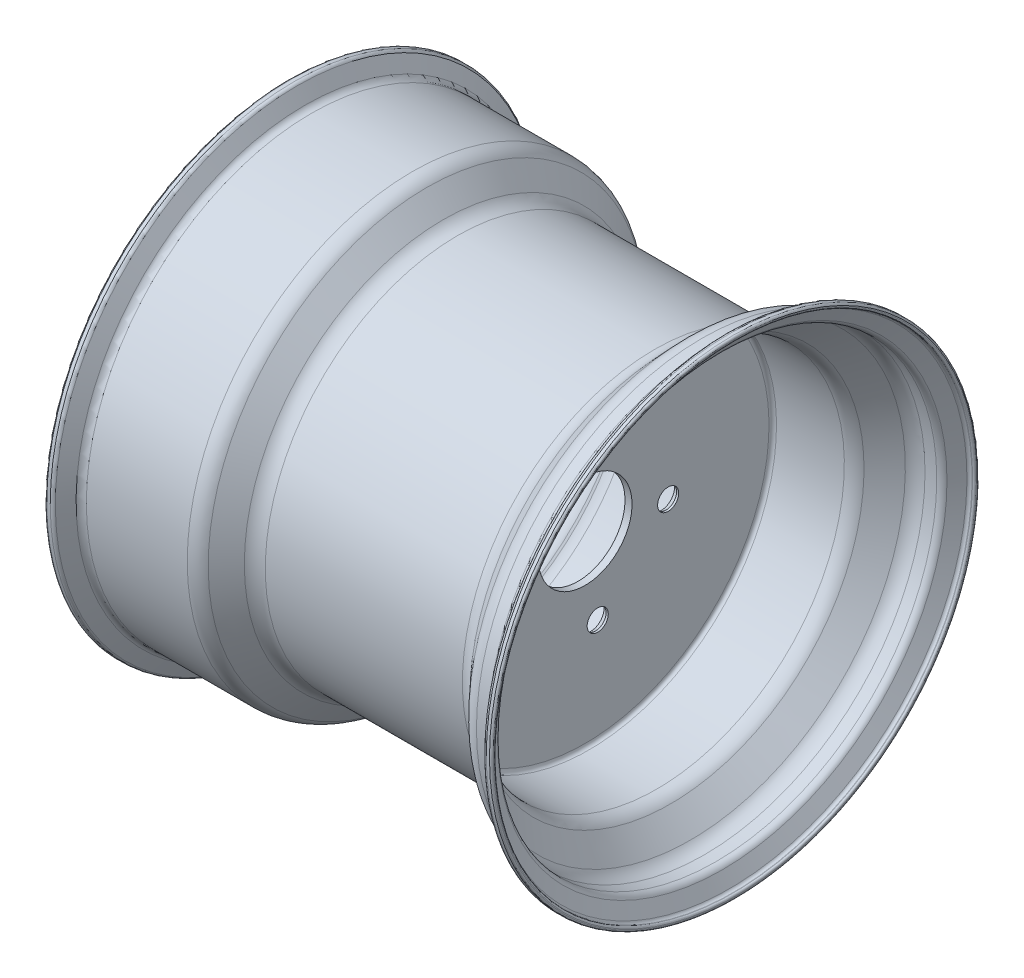
SolidWorks part; units mm, degrees
material "1060 Alloy"
ref_plane "Front Plane" through (0, 0, 0) normal (0, 0, 1) x (1, 0, 0)
ref_plane "Top Plane" through (0, 0, 0) normal (0, 1, 0) x (1, 0, 0)
ref_plane "Right Plane" through (0, 0, 0) normal (1, 0, 0) x (0, 0, -1)
sketch "Sketch1" plane through (0, 0, 0) normal (0, 0, 1) x (1, 0, 0)
  line L0 (-81.5771, 130.175) -> (51.8349, 130.175)
  line L2 (0, 124.46) -> (0, 0)
  line L3 (-84.533, 127) -> (-2.54, 127)
  line L4 (-105.4345, 144.7317) -> (-94.2253, 131.4933)
  line L5 (-182.3188, 149.225) -> (-115.1268, 149.225)
  line L6 (-102.4786, 147.9067) -> (-91.2694, 134.6683)
  line L7 (-194.5586, 161.925) -> (-194.0506, 161.925)
  line L8 (-195.8286, 163.83) -> (-195.8286, 163.195)
  line L9 (-192.2175, 165.1) -> (-194.5586, 165.1)
  line L10 (-184.8852, 154.94) -> (-190.0178, 163.83)
  line L11 (-112.1709, 152.4) -> (-180.4858, 152.4)
  line L12 (61.123, 134.2136) -> (74.6121, 148.6789)
  line L13 (83.9003, 152.7175) -> (91.3853, 152.7175)
  line L14 (95.7847, 155.2575) -> (100.734, 163.83)
  line L15 (102.9337, 165.1) -> (105.0925, 165.1)
  line L16 (106.3625, 163.83) -> (106.3625, 163.195)
  line L17 (105.0925, 161.925) -> (104.7668, 161.925)
  line L18 (102.5671, 160.655) -> (97.6177, 152.0825)
  line L19 (93.2183, 149.5425) -> (85.2808, 149.5425)
  line L20 (75.9926, 145.5039) -> (62.5036, 131.0386)
  line L21 (53.2154, 127) -> (7.3025, 127)
  line L22 (4.7625, 124.46) -> (4.7625, 0)
  line L23 (4.7625, 0) -> (0, 0)
  line L26 (-191.8509, 160.655) -> (-186.7182, 151.765)
  arc A0 (106.3625, 163.195) -> (105.0925, 161.925) centre (105.0925, 163.195) cw
  arc A1 (105.0925, 165.1) -> (106.3625, 163.83) centre (105.0925, 163.83) cw
  arc A2 (-194.5586, 161.925) -> (-195.8286, 163.195) centre (-194.5586, 163.195) cw
  arc A3 (-195.8286, 163.83) -> (-194.5586, 165.1) centre (-194.5586, 163.83) cw
  arc A4 (-192.2175, 165.1) -> (-190.0178, 163.83) centre (-192.2175, 162.56) cw
  arc A5 (-191.8509, 160.655) -> (-194.0506, 161.925) centre (-194.0506, 159.385) ccw
  arc A6 (104.7668, 161.925) -> (102.5671, 160.655) centre (104.7668, 159.385) ccw
  arc A7 (100.734, 163.83) -> (102.9337, 165.1) centre (102.9337, 162.56) cw
  arc A8 (62.5036, 131.0386) -> (53.2154, 127) centre (53.2154, 139.7) cw
  arc A9 (51.8349, 130.175) -> (61.123, 134.2136) centre (51.8349, 142.875) ccw
  arc A10 (74.6121, 148.6789) -> (83.9003, 152.7175) centre (83.9003, 140.0175) cw
  arc A11 (85.2808, 149.5425) -> (75.9926, 145.5039) centre (85.2808, 136.8425) ccw
  arc A12 (97.6177, 152.0825) -> (93.2183, 149.5425) centre (93.2183, 154.6225) cw
  arc A13 (91.3853, 152.7175) -> (95.7847, 155.2575) centre (91.3853, 157.7975) ccw
  arc A14 (-102.4786, 147.9067) -> (-112.1709, 152.4) centre (-112.1709, 139.7) ccw
  arc A15 (-184.8852, 154.94) -> (-180.4858, 152.4) centre (-180.4858, 157.48) ccw
  arc A16 (-81.5771, 130.175) -> (-91.2694, 134.6683) centre (-81.5771, 142.875) cw
  arc A17 (-84.533, 127) -> (-94.2253, 131.4933) centre (-84.533, 139.7) cw
  arc A18 (-105.4345, 144.7317) -> (-115.1268, 149.225) centre (-115.1268, 136.525) ccw
  arc A20 (7.3025, 127) -> (4.7625, 124.46) centre (7.3025, 124.46) ccw
  arc A21 (0, 124.46) -> (-2.54, 127) centre (-2.54, 124.46) ccw
  arc A22 (-182.3188, 149.225) -> (-186.7182, 151.765) centre (-182.3188, 154.305) cw
  point P29 (106.3625, 161.925)
  point P32 (106.3625, 165.1)
  point P43 (103.3003, 161.925)
  point P48 (58.7375, 127)
  point P53 (78.3782, 152.7175)
  point P56 (79.7587, 149.5425)
  point P59 (96.1513, 149.5425)
  point P62 (94.3182, 152.7175)
  point P68 (-183.4187, 152.4)
  point P71 (-98.4276, 130.175)
  point P74 (-90.4207, 127)
  point P77 (-109.2391, 149.225)
  point P83 (4.7625, 127)
  point P86 (0, 127)
  dimension "D14" = 1.27
  dimension "D15" = 2.54
  dimension "D16" = 12.7
  dimension "D17" = 5.08
  dimension "D20" = 0.508
  dimension "D21" = 3.175
  dimension "D22" = 2.54
  dimension "D25" = 5.08
  dimension "D18" = 2.54
  dimension "D26" = 5.08
  dimension "D28" = 2.54
  dimension "D13" = 12.7
  dimension "D1" = 3.175
  dimension "D2" = 101.6
  dimension "D3" = 120
  dimension "D4" = 53.975
  dimension "D5" = 7.9375
  dimension "D6" = 3.175
  dimension "D7" = 3.175
  dimension "D8" = 3.175
  dimension "D9" = 22.5425
  dimension "D10" = 165.1
  dimension "D11" = 127
  dimension "D12" = 4.7625
  dimension "D19" = 120
  dimension "D23" = 280.67
  dimension "D24" = 3.175
  dimension "D27" = 3.175
  dimension "D29" = 12.3825
  dimension "D30" = 12.7
  dimension "D31" = 3.175
  dimension "D32" = 165.1
  dimension "D33" = 3.175
  dimension "D34" = 133
  dimension "D35" = 4.3075
revolve "Revolve1" add sketch "Sketch1" angle 360 about L23
sketch "Sketch2" plane through (0, 0, 0) normal (-1, 0, 0) x (0, 0, 1)
  line L0 (-44.9914, 69.0815) -> (68.5343, -42.8561) construction
  line L1 (-48.8875, 36.056) -> (13.8992, 99.7335) construction
  circle A0 centre (-26.2167, 50.5695) radius 5.9531
  circle A1 centre (39.9931, 40.5604) radius 5.9531
  circle A2 centre (50.9338, -25.5018) radius 5.9531
  circle A3 centre (-8.5142, -56.3214) radius 5.9531
  circle A4 centre (-56.1959, -9.3067) radius 5.9531
  circle A5 centre (0, 0) radius 31.75
  circle A6 centre (-26.2167, 50.5695) radius 7.1438
  circle A7 centre (0, 0) radius 31.75
  circle A8 centre (39.9931, 40.5604) radius 7.1438
  circle A9 centre (0, 0) radius 31.75
  circle A10 centre (50.9338, -25.5018) radius 7.1437
  circle A11 centre (0, 0) radius 31.75
  circle A12 centre (-8.5142, -56.3214) radius 7.1438
  circle A13 centre (0, 0) radius 31.75
  circle A14 centre (-56.1959, -9.3067) radius 7.1438
  point P13 (0, 0)
  point P33 (0, 0)
  dimension "D1" = 5
  dimension "D2" = 11.9062
  dimension "D4" = 14.2875
  dimension "D3" = 114.3
  dimension "D5" = 5
extrude "Cut-Extrude1" cut sketch "Sketch2" against normal up to next contours A5 | A14 A4 | A6 A0 | A0 | A1 | A8 A1 | A10 | A12
chamfer "Chamfer1" distance 1.905 angle 60 5 edges at (0, 40.5604, 47.1368) (0, -25.5018, 58.0775) (0, -56.3214, -1.3705) (0, -9.3067, -49.0521) (0, 50.5695, -19.073)
